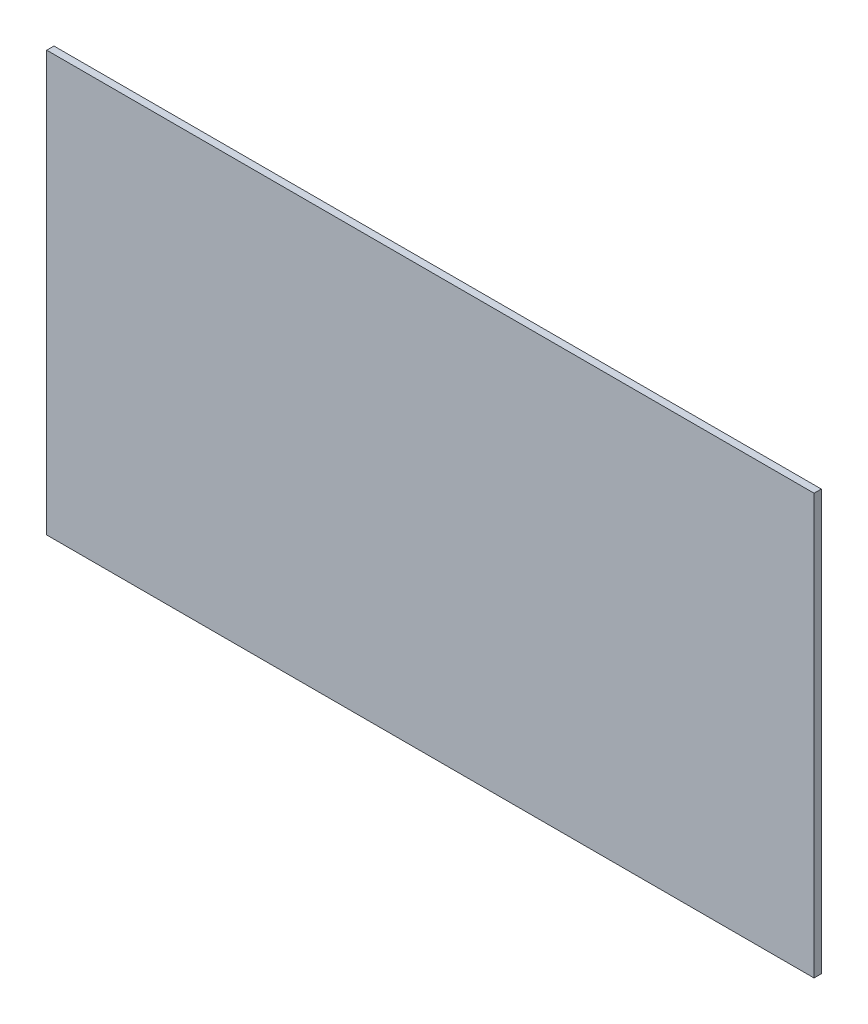
SolidWorks part; units mm, degrees
material "PE Low Density Film"
ref_plane "Front Plane" through (0, 0, 0) normal (0, 0, 1) x (1, 0, 0)
ref_plane "Top Plane" through (0, 0, 0) normal (0, 1, 0) x (1, 0, 0)
ref_plane "Right Plane" through (0, 0, 0) normal (1, 0, 0) x (0, 0, -1)
sketch "Sketch1" plane through (0, 0, 0) normal (0, 0, 1) x (1, 0, 0)
  line L8 (-87.7427, -16.1854) -> (-101.2047, -16.1854)
  line L9 (-101.2047, -16.1854) -> (-101.2047, -23.5514)
  line L10 (-101.2047, -23.5514) -> (-87.7427, -23.5514)
  line L11 (-87.7427, -23.5514) -> (-87.7427, -16.1854)
extrude "Boss-Extrude1" add sketch "Sketch1" along normal blind 0.127
